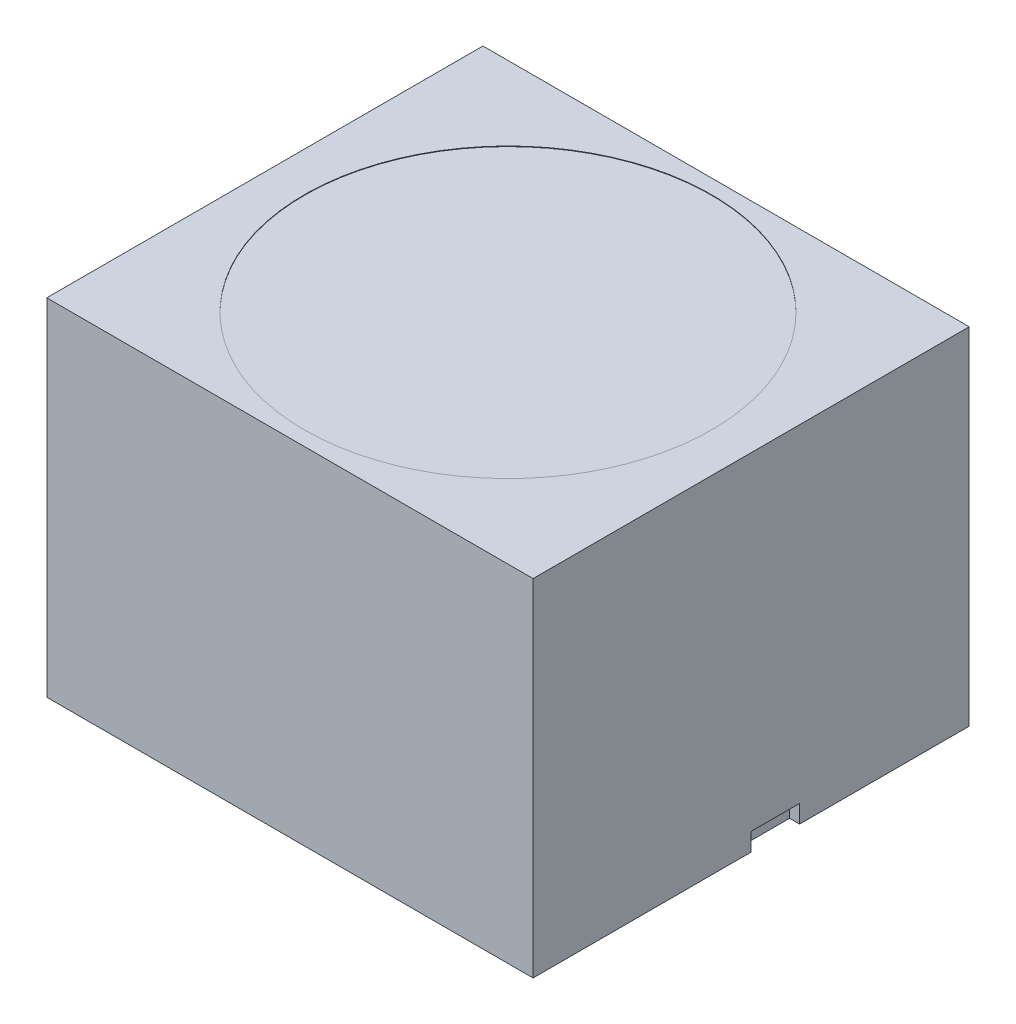
SolidWorks part; units mm, degrees
ref_plane "Alzado" through (0, 0, 0) normal (0, 0, 1) x (1, 0, 0)
ref_plane "Planta" through (0, 0, 0) normal (0, 1, 0) x (1, 0, 0)
ref_plane "Vista lateral" through (0, 0, 0) normal (1, 0, 0) x (0, 0, -1)
sketch "Croquis1" plane through (0, 0, 0) normal (0, 1, 0) x (1, 0, 0)
  line L1 (-48.5, -43.5) -> (48.5, -43.5)
  line L2 (-48.5, -43.5) -> (-48.5, 43.5)
  line L3 (-48.5, 43.5) -> (48.5, 43.5)
  line L4 (48.5, -43.5) -> (48.5, 43.5)
  line L5 (-48.5, -43.5) -> (48.5, 43.5) construction
  line L6 (-48.5, 43.5) -> (48.5, -43.5) construction
  point P0 (0, 0)
  dimension "D1" = 97
  dimension "D2" = 87
extrude "Saliente-Extruir1" add sketch "Croquis1" along normal blind 69
sketch "Croquis2" plane through (0, 69, 0) normal (0, 1, 0) x (1, 0, 0)
  circle A0 centre (0, 0) radius 40.6258
extrude "Cortar-Extruir1" cut sketch "Croquis2" against normal blind 0.1
sketch "Croquis3" plane through (48.5, 0, 0) normal (1, 0, 0) x (0, 0, -1)
  line L1 (0, 0) -> (9.6717, 0)
  line L2 (0, 0) -> (0, 3.5784)
  line L3 (0, 3.5784) -> (9.6717, 3.5784)
  line L4 (9.6717, 0) -> (9.6717, 3.5784)
extrude "Cortar-Extruir2" cut sketch "Croquis3" against normal blind 2
